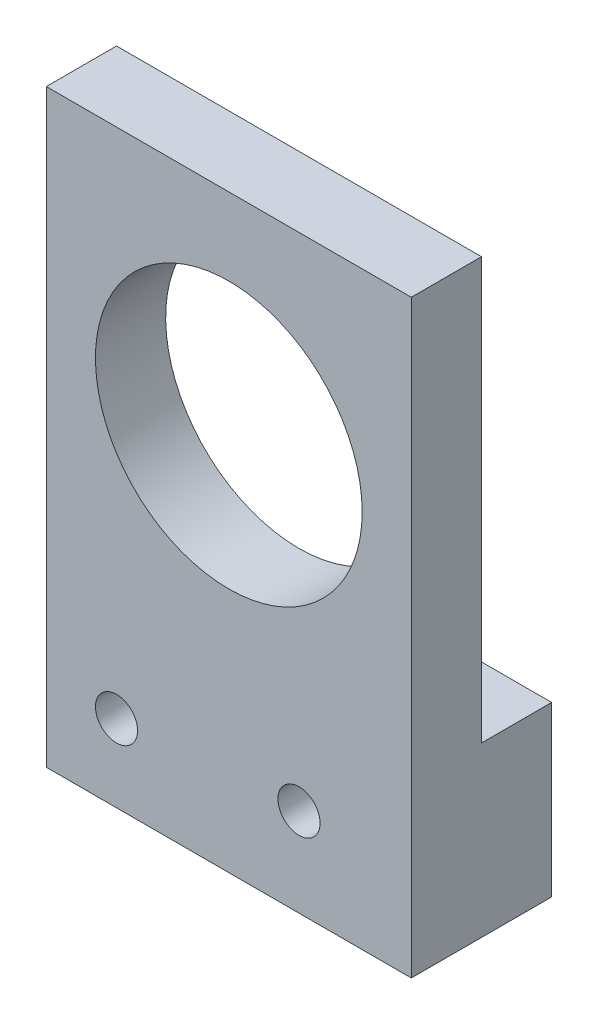
SolidWorks part; units mm, degrees
ref_plane "Front Plane" through (0, 0, 0) normal (0, 0, 1) x (1, 0, 0)
ref_plane "Top Plane" through (0, 0, 0) normal (0, 1, 0) x (1, 0, 0)
ref_plane "Right Plane" through (0, 0, 0) normal (1, 0, 0) x (0, 0, -1)
sketch "Croquis1" plane through (0, 0, 0) normal (0, 0, 1) x (1, 0, 0)
  line L0 (-13, -27) -> (-13, 15)
  line L1 (-13, 15) -> (13, 15)
  line L2 (13, 15) -> (13, -27)
  line L3 (13, -27) -> (-13, -27)
  line L4 (0, 0) -> (0, -26.9482) construction
  circle A0 centre (0, 0) radius 9.5
  circle A1 centre (-8, -21.5) radius 1.5
  circle A2 centre (5, -20.7) radius 1.5
  point P12 (0, 0)
  dimension "D1" = 19
  dimension "D2" = 13
  dimension "D6" = 3
  dimension "D7" = 21.5
  dimension "D9" = 3
  dimension "D10" = 5
  dimension "D3" = 13
  dimension "D4" = 42
  dimension "D5" = 27
  dimension "D8" = 20.7
  dimension "D11" = 5
extrude "Saliente-Extruir1" add sketch "Croquis1" along normal blind 10
sketch "Croquis2" plane through (-13, 0, 0) normal (-1, 0, 0) x (0, 0, 1)
  line L0 (0, 15) -> (5, 15)
  line L1 (10, 15) -> (0, 15) construction
  line L2 (5, 15) -> (5, -15)
  line L3 (5, -15) -> (0, -15)
  line L4 (0, 15) -> (0, -27) construction
  line L5 (0, 15) -> (0, -15)
  dimension "D1" = 30
extrude "Cortar-Extruir1" cut sketch "Croquis2" against normal blind 40
